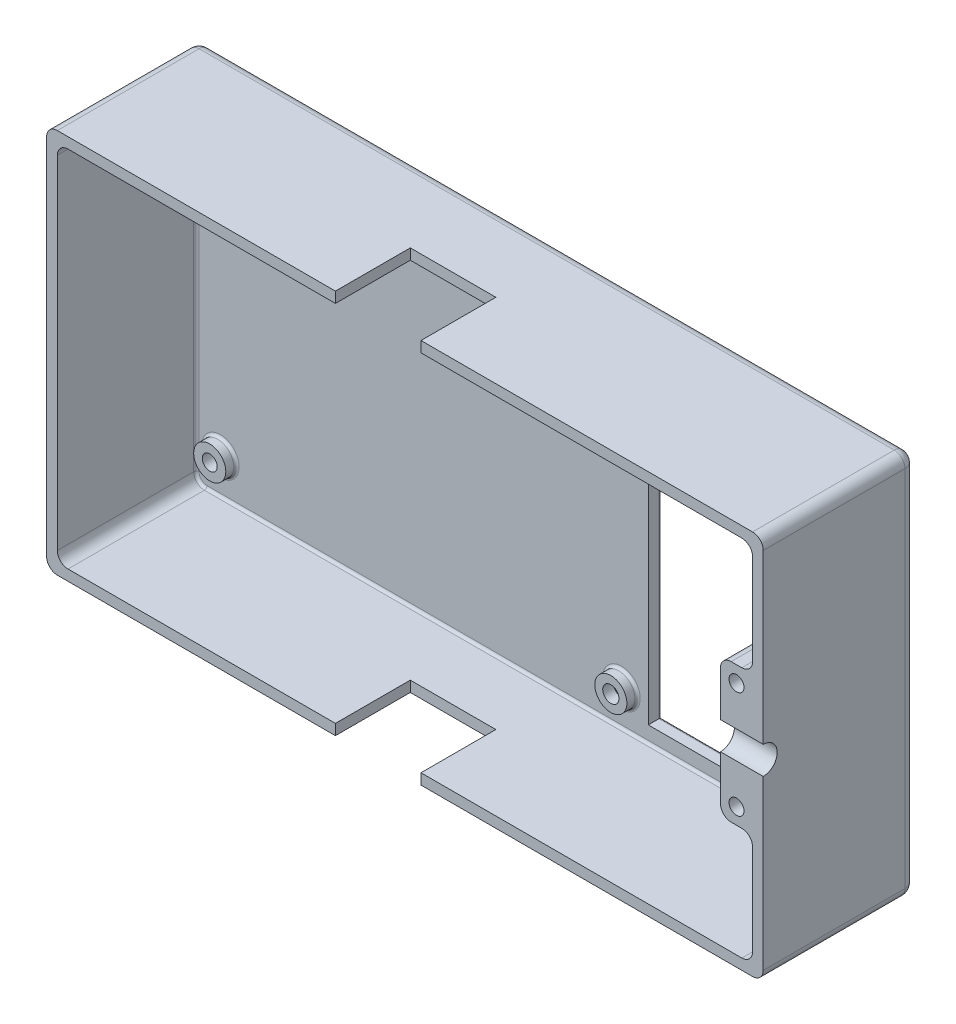
SolidWorks part; units mm, degrees
ref_plane "Front" through (0, 0, 0) normal (0, 0, 1) x (1, 0, 0)
ref_plane "Top" through (0, 0, 0) normal (0, 1, 0) x (1, 0, 0)
ref_plane "Right" through (0, 0, 0) normal (1, 0, 0) x (0, 0, -1)
sketch "Эскиз1" plane through (0, 0, 0) normal (0, 0, 1) x (1, 0, 0)
  line L0 (-71.8141, 24.0145) -> (62.1859, 24.0145)
  line L1 (62.1859, 24.0145) -> (62.1859, -47.9855)
  line L2 (62.1859, -47.9855) -> (-71.8141, -47.9855)
  line L3 (-71.8141, -47.9855) -> (-71.8141, 24.0145)
  line L4 (-67.8141, 24.0145) -> (-67.8141, 20.0145) construction
  line L5 (-67.8141, 20.0145) -> (-67.8141, -43.9855) construction
  line L6 (-67.8141, -43.9855) -> (-67.8141, -47.9855) construction
  line L7 (-67.8141, 20.0145) -> (-71.8141, 20.0145) construction
  line L8 (-67.8141, 20.0145) -> (12.1859, 20.0145) construction
  line L9 (12.1859, 20.0145) -> (12.1859, -43.9855) construction
  line L10 (12.1859, -43.9855) -> (-67.8141, -43.9855) construction
  line L11 (12.1859, 20.0145) -> (54.1859, 20.0145) construction
  line L12 (54.1859, 20.0145) -> (62.1859, 20.0145) construction
  line L13 (54.1859, 20.0145) -> (54.1859, -43.9855) construction
  line L14 (54.1859, -43.9855) -> (12.1859, -43.9855) construction
  line L15 (14.6859, 20.0145) -> (14.6859, 19.0145) construction
  line L16 (14.6859, 19.0145) -> (51.6859, 19.0145)
  line L17 (14.6859, -42.9855) -> (14.6859, -43.9855) construction
  line L18 (12.1859, 19.0145) -> (14.6859, 19.0145) construction
  line L19 (51.6859, 19.0145) -> (51.6859, -42.9855)
  line L20 (51.6859, 19.0145) -> (54.1859, 19.0145) construction
  line L21 (51.6859, -42.9855) -> (14.6859, -42.9855)
  line L22 (14.6859, -42.9855) -> (14.6859, 19.0145)
  line L23 (-67.8141, 15.5145) -> (-65.3141, 15.5145) construction
  line L24 (-65.3141, 15.5145) -> (9.6859, 15.5145) construction
  line L25 (9.6859, 15.5145) -> (12.1859, 15.5145) construction
  line L26 (-65.3141, 20.0145) -> (-65.3141, 15.5145) construction
  line L27 (-65.3141, 15.5145) -> (-65.3141, -39.4855) construction
  line L28 (-65.3141, -39.4855) -> (-65.3141, -43.9855) construction
  line L29 (-65.3141, -39.4855) -> (9.6859, -39.4855) construction
  line L30 (9.6859, -39.4855) -> (9.6859, 15.5145) construction
  line L31 (57.1859, 20.0145) -> (57.1859, 15.5145) construction
  line L32 (57.1859, 15.5145) -> (57.1859, -1.9855) construction
  line L33 (57.1859, -1.9855) -> (57.1859, -11.9855) construction
  line L34 (57.1859, -11.9855) -> (57.1859, -21.9855) construction
  line L35 (57.1859, -21.9855) -> (57.1859, -39.4855) construction
  line L36 (57.1859, -39.4855) -> (57.1859, -43.9855) construction
  line L37 (57.1859, -43.9855) -> (54.1859, -43.9855) construction
  line L38 (12.1859, 15.5145) -> (57.1859, 15.5145) construction
  line L39 (57.1859, -39.4855) -> (54.1859, -39.4855) construction
  circle A0 centre (-65.3141, 15.5145) radius 1.4
  circle A1 centre (9.6859, 15.5145) radius 1.4
  circle A2 centre (9.6859, -39.4855) radius 1.4
  circle A3 centre (-65.3141, -39.4855) radius 1.4
  circle A4 centre (57.1859, 15.5145) radius 1.4
  circle A6 centre (57.1859, -39.4855) radius 1.4
  circle A7 centre (57.1859, -1.9855) radius 1.4
  circle A8 centre (57.1859, -21.9855) radius 1.4
  dimension "D8" = 75
  dimension "D11" = 10
  dimension "D1" = 64
  dimension "D2" = 4
  dimension "D3" = 80
  dimension "D4" = 8
  dimension "D5" = 42
  dimension "D6" = 37
  dimension "D7" = 62
  dimension "D9" = 55
  dimension "D10" = 3
extrude "Бобышка-Вытянуть1" add sketch "Эскиз1" along normal blind 2.5
sketch "Эскиз2" plane through (0, 0, 2.5) normal (0, 0, 1) x (1, 0, 0)
  line L0 (-71.8141, 24.0145) -> (62.1859, 24.0145)
  line L1 (62.1859, 24.0145) -> (62.1859, -47.9855)
  line L2 (62.1859, -47.9855) -> (-71.8141, -47.9855)
  line L3 (-71.8141, -47.9855) -> (-71.8141, 24.0145)
  line L4 (-69.8141, 24.0145) -> (-69.8141, 22.0145) construction
  line L5 (-69.8141, 22.0145) -> (-71.8141, 22.0145) construction
  line L6 (-69.8141, -47.9855) -> (-69.8141, -45.9855) construction
  line L7 (-69.8141, -45.9855) -> (-71.8141, -45.9855) construction
  line L8 (-69.8141, 22.0145) -> (60.1859, 22.0145)
  line L10 (60.1859, -45.9855) -> (-69.8141, -45.9855)
  line L11 (-69.8141, -45.9855) -> (-69.8141, 22.0145)
  line L12 (60.1859, 22.0145) -> (62.1859, 22.0145) construction
  line L13 (60.1859, 22.0145) -> (60.1859, 1.0145)
  line L14 (60.1859, 1.0145) -> (54.1859, 1.0145)
  line L15 (54.1859, 1.0145) -> (54.1859, -24.9855)
  line L16 (54.1859, -24.9855) -> (60.1859, -24.9855)
  line L17 (60.1859, -24.9855) -> (60.1859, -45.9855)
  circle A0 centre (57.1859, -1.9855) radius 1.4
  circle A1 centre (57.1859, -21.9855) radius 1.4
  dimension "D1" = 2
  dimension "D2" = 2
  dimension "D3" = 6
  dimension "D4" = 26
extrude "Бобышка-Вытянуть2" add sketch "Эскиз2" along normal blind 26
sketch "Эскиз3" plane through (62.1859, 0, 0) normal (1, 0, 0) x (0, 0, -1)
  line L0 (-28.5, -47.9855) -> (-28.5, 24.0145) construction
  circle A0 centre (-28.5, -11.9855) radius 2.6
extrude "Вырез-Вытянуть1" cut sketch "Эскиз3" against normal blind 26
sketch "Эскиз4" plane through (0, -47.9855, 0) normal (0, -1, 0) x (1, 0, 0)
  line L0 (-17.8141, 28.5) -> (-17.8141, 14.5)
  line L1 (-71.8141, 28.5) -> (62.1859, 28.5) construction
  line L2 (-17.8141, 14.5) -> (-1.8141, 14.5)
  line L3 (-1.8141, 14.5) -> (-1.8141, 28.5)
  line L4 (-1.8141, 28.5) -> (-17.8141, 28.5)
  line L5 (-71.8141, 14.5) -> (-17.8141, 14.5) construction
  line L6 (-71.8141, 28.5) -> (-71.8141, 0) construction
  line L7 (-17.8141, 0) -> (-17.8141, 14.5) construction
  line L8 (-71.8141, 0) -> (62.1859, 0) construction
  dimension "D1" = 16
  dimension "D2" = 14.5
  dimension "D3" = 54
extrude "Вырез-Вытянуть2" cut sketch "Эскиз4" against normal blind 26
sketch "Эскиз5" plane through (0, 0, 2.5) normal (0, 0, 1) x (1, 0, 0)
  circle A0 centre (-65.3141, 15.5145) radius 1.4
  circle A1 centre (-65.3141, 15.5145) radius 3
  circle A2 centre (9.6859, 15.5145) radius 1.4
  circle A3 centre (9.6859, -39.4855) radius 1.5172
  circle A4 centre (-65.3141, -39.4855) radius 1.4
  circle A5 centre (9.6859, 15.5145) radius 3
  circle A6 centre (9.6859, -39.4855) radius 3
  circle A7 centre (-65.3141, -39.4855) radius 3
  circle A8 centre (57.1859, 15.5145) radius 1.4
  circle A9 centre (57.1859, -39.4855) radius 1.4
  circle A10 centre (57.1859, -39.4855) radius 3.1
  circle A11 centre (57.1859, 15.5145) radius 3.1
extrude "Бобышка-Вытянуть4" add sketch "Эскиз5" along normal blind 2
fillet "Скругление1" radius 2 4 edges at (62.1859, 24.0145, 14.25) (62.1859, -47.9855, 14.25) (-71.8141, -47.9855, 14.25) (-71.8141, 24.0145, 14.25)
fillet "Скругление2" radius 2 8 edges at (-69.8141, -45.9855, 15.5) (-69.8141, 22.0145, 15.5) (60.1859, -24.9855, 15.5) (60.1859, 22.0145, 15.5) (54.1859, -24.9855, 15.5) (54.1859, 1.0145, 15.5) (60.1859, 1.0145, 15.5) (60.1859, -45.9855, 15.5)
fillet "Скругление3" radius 0.5 24 edges at (60.1859, 8.874, 2.5) (59.6001, 1.6003, 2.5) (57.1859, 1.0145, 2.5) (54.7717, 0.4287, 2.5) (54.1859, -11.9855, 2.5) (54.7717, -24.3997, 2.5) (57.1859, -24.9855, 2.5) (59.6001, -25.5713, 2.5) (60.1859, 18.155, 2.5) (59.6001, 21.4287, 2.5) (-4.8141, 22.0145, 2.5) (-69.2283, 21.4287, 2.5) (-69.8141, -11.9855, 2.5) (-69.2283, -45.3997, 2.5) (60.1859, -42.126, 2.5) (59.6001, -45.3997, 2.5) (60.1859, -32.845, 2.5) (-4.8141, -45.9855, 2.5) (54.0859, -39.4855, 2.5) (54.0859, 15.5145, 2.5) (6.6859, 15.5145, 2.5) (-68.3141, 15.5145, 2.5) (6.6859, -39.4855, 2.5) (-68.3141, -39.4855, 2.5)
fillet "Скругление4" radius 2 8 edges at (61.6001, 23.4287, 0) (62.1859, -11.9855, 0) (61.6001, -47.3997, 0) (-4.8141, -47.9855, 0) (-71.2283, -47.3997, 0) (-71.8141, -11.9855, 0) (-71.2283, 23.4287, 0) (-4.8141, 24.0145, 0)
fillet "Скругление5" radius 0.5 12 edges at (58.5859, -21.9855, 0) (58.5859, -39.4855, 0) (-63.9141, -39.4855, 0) (11.0859, 15.5145, 0) (51.6859, -11.9855, 0) (33.1859, -42.9855, 0) (14.6859, -11.9855, 0) (33.1859, 19.0145, 0) (-63.9141, 15.5145, 0) (11.0859, -39.4855, 0) (58.5859, 15.5145, 0) (58.5859, -1.9855, 0)
sketch "Эскиз6" plane through (0, 24.0145, 0) normal (0, 1, 0) x (1, 0, 0)
  line L0 (-17.8141, -28.5) -> (-17.8141, -14.5)
  line L1 (60.1859, -28.5) -> (-69.8141, -28.5) construction
  line L2 (-17.8141, -14.5) -> (-1.8141, -14.5)
  line L3 (-1.8141, -14.5) -> (-1.8141, -28.5)
  line L4 (-1.8141, -28.5) -> (-17.8141, -28.5)
  line L5 (-17.8141, -14.5) -> (-71.8141, -14.5) construction
  line L7 (-17.8141, -14.5) -> (-17.8141, 0) construction
  line L8 (-69.8141, 0) -> (60.1859, 0) construction
  line L9 (-71.8141, -28.5) -> (-71.8141, -2) construction
  dimension "D1" = 16
  dimension "D2" = 14.5
  dimension "D3" = 54
extrude "Вырез-Вытянуть3" cut sketch "Эскиз6" against normal blind 2
